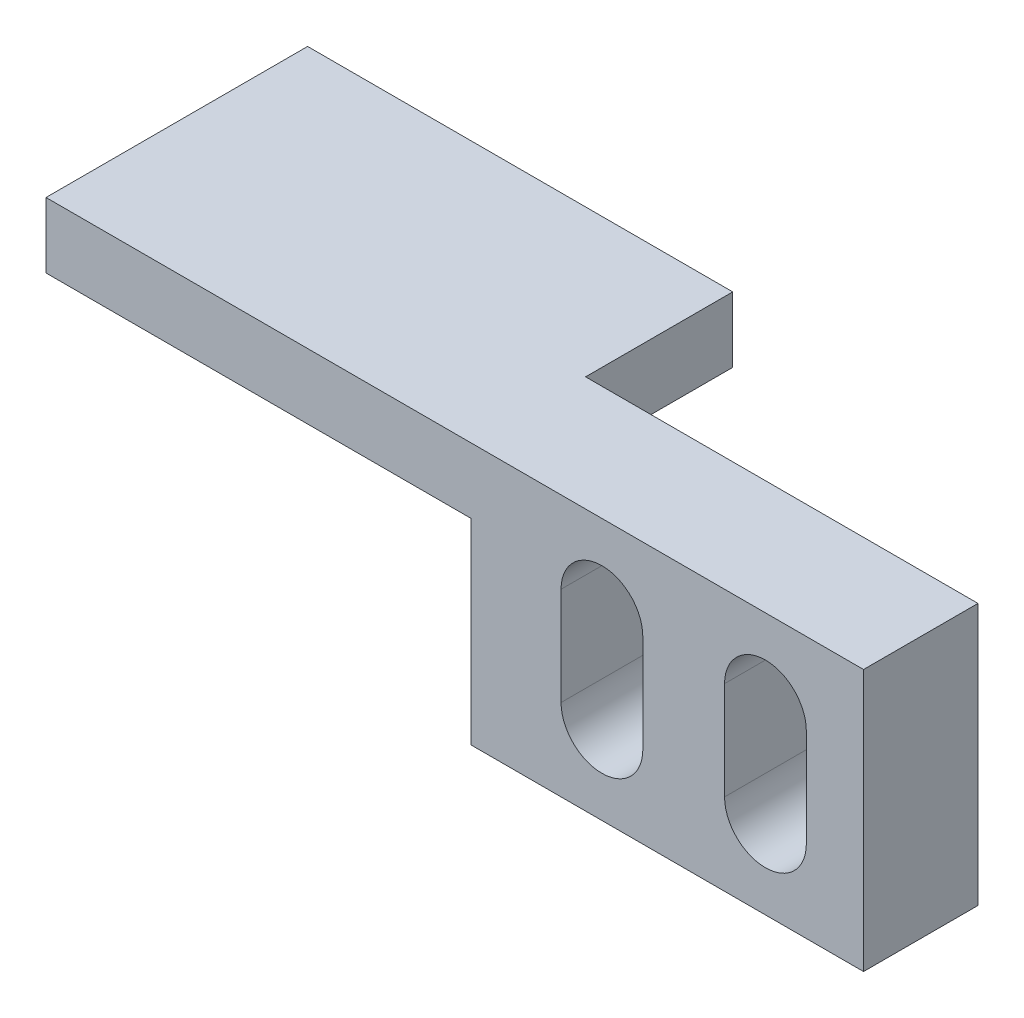
SolidWorks part; units mm, degrees
ref_plane "Front Plane" through (0, 0, 0) normal (0, 0, 1) x (1, 0, 0)
ref_plane "Top Plane" through (0, 0, 0) normal (0, 1, 0) x (1, 0, 0)
ref_plane "Right Plane" through (0, 0, 0) normal (1, 0, 0) x (0, 0, -1)
sketch "Sketch1" plane through (0, 0, 0) normal (0, 0, 1) x (1, 0, 0)
  line L1 (0, 0) -> (12, 0)
  line L2 (0, 0) -> (0, 8)
  line L3 (0, 8) -> (12, 8)
  line L4 (12, 0) -> (12, 8)
  dimension "D1" = 12
  dimension "D2" = 8
extrude "Boss-Extrude1" add sketch "Sketch1" along normal blind 3.5
sketch "Sketch2" plane through (0, 0, 3.5) normal (0, 0, 1) x (1, 0, 0)
  line L0 (4, 5.5) -> (4, 2.5) construction
  line L1 (5.25, 5.5) -> (5.25, 2.5)
  line L2 (2.75, 5.5) -> (2.75, 2.5)
  line L3 (9, 5.5) -> (9, 2.5) construction
  line L4 (10.25, 5.5) -> (10.25, 2.5)
  line L5 (7.75, 5.5) -> (7.75, 2.5)
  line L6 (12, 8) -> (0, 8) construction
  line L7 (12, 0) -> (12, 8) construction
  arc A0 (5.25, 5.5) -> (2.75, 5.5) centre (4, 5.5) ccw
  arc A1 (2.75, 2.5) -> (5.25, 2.5) centre (4, 2.5) ccw
  arc A2 (10.25, 5.5) -> (7.75, 5.5) centre (9, 5.5) ccw
  arc A3 (7.75, 2.5) -> (10.25, 2.5) centre (9, 2.5) ccw
  point P2 (4, 4)
  point P7 (9, 4)
  dimension "D1" = 1.25
  dimension "D3" = 2.5
  dimension "D2" = 3
  dimension "D4" = 1.75
  dimension "D5" = 2.5
extrude "Cut-Extrude1" cut sketch "Sketch2" against normal through all
sketch "Sketch3" plane through (0, 0, 0) normal (-1, 0, 0) x (0, 0, 1)
  line L0 (3.5, 8) -> (3.5, 0) construction
  line L1 (0, 8) -> (3.5, 8)
  line L2 (0, 8) -> (0, 6)
  line L3 (0, 6) -> (3.5, 6)
  line L4 (3.5, 8) -> (3.5, 6)
  dimension "D1" = 2
extrude "Boss-Extrude2" add sketch "Sketch3" along normal blind 13
sketch "Sketch4" plane through (0, 0, 0) normal (0, 0, -1) x (-1, 0, 0)
  line L1 (0, 6) -> (13, 6)
  line L2 (0, 6) -> (0, 8)
  line L3 (0, 8) -> (13, 8)
  line L4 (13, 6) -> (13, 8)
extrude "Boss-Extrude3" add sketch "Sketch4" along normal blind 4.5
